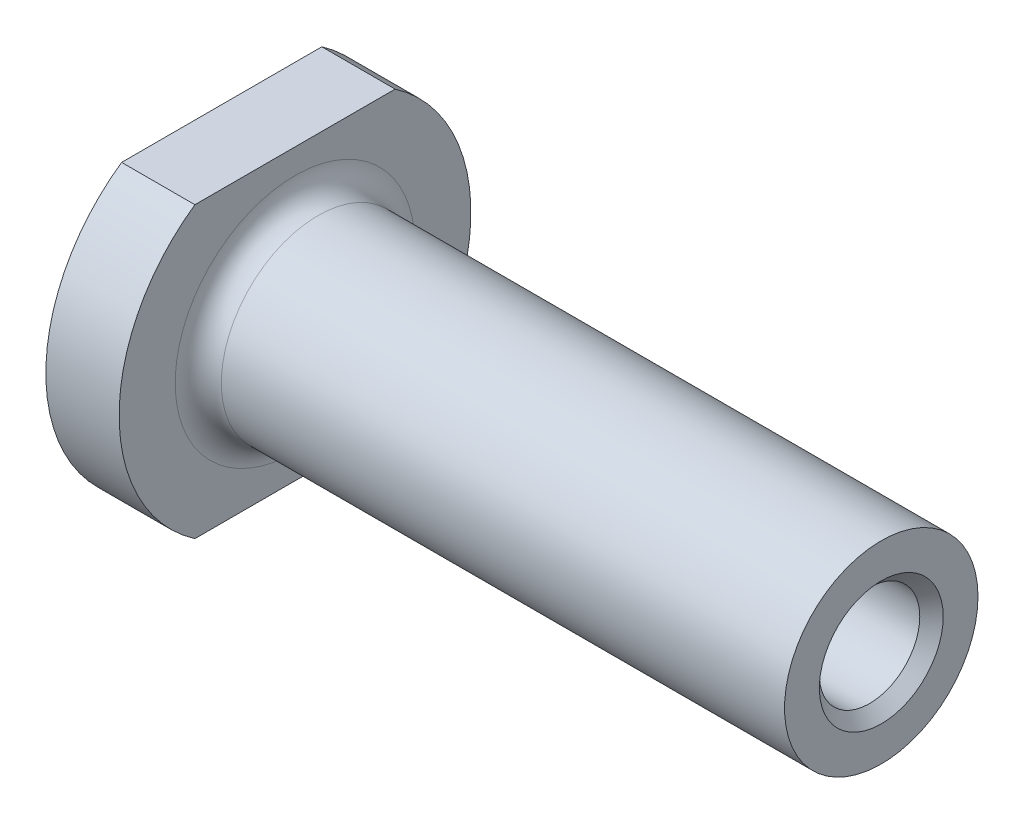
SolidWorks part; units mm, degrees
material "Alloy Steel"
ref_plane "Front Plane" through (0, 0, 0) normal (0, 0, 1) x (1, 0, 0)
ref_plane "Top Plane" through (0, 0, 0) normal (0, 1, 0) x (1, 0, 0)
ref_plane "Right Plane" through (0, 0, 0) normal (1, 0, 0) x (0, 0, -1)
sketch "Sketch1" plane through (0, 0, 0) normal (0, 0, 1) x (1, 0, 0)
  line L0 (0, 0) -> (-17.6508, 0) construction
  line L1 (0, 0) -> (42.8625, 0)
  line L2 (42.8625, 0) -> (42.8625, 6.2865)
  line L3 (42.8625, 6.2865) -> (4.7625, 6.2865)
  line L4 (4.7625, 6.2865) -> (4.7625, 11.43)
  line L5 (4.7625, 11.43) -> (0, 11.43)
  line L6 (0, 11.43) -> (0, 0)
  dimension "D1" = 12.573
  dimension "D2" = 42.8625
  dimension "D3" = 4.7625
  dimension "D4" = 22.86
revolve "Revolve1" add sketch "Sketch1" angle 360 about L0
fillet "Fillet1" radius 1.5 1 edges at (4.7625, 0, -6.2865)
hole_wizard "5/16-18" positions "Sketch2" profile "Sketch3" tap size "5/16-18" standard "ANSI Inch" end condition through all
sketch "Sketch2" plane through (42.8625, 0, 0) normal (1, 0, 0) x (0, 0, -1)
  point P0 (0, 0)
sketch "Sketch3" plane through (42.8625, 0, 0) normal (0, 1, 0) x (0, 0, -1)
  line L0 (0, 0) -> (0, 42.8625)
  line L1 (0, 42.8625) -> (3.2639, 42.8625)
  line L2 (3.2639, 42.8625) -> (3.2639, 0)
  line L5 (3.2639, 0) -> (0, 0)
  line L11 (0, -6.35) -> (0, 107.95) construction
  dimension "Thru Tap Drill Dia." = 6.5278
  dimension "Thru Tap Drill Depth" = 42.8625
cosmetic thread "Hole Thread1" parameters "D2"=7.9375
sketch "Sketch4" plane through (0, 0, 0) normal (-1, 0, 0) x (0, 0, 1)
  line L0 (-6.5056, 9.398) -> (6.5056, 9.398)
  line L5 (6.5056, -9.398) -> (-6.5056, -9.398)
  arc A1 (6.5056, 9.398) -> (-6.5056, 9.398) centre (0, 0) ccw
  circle A2 centre (0, 0) radius 11.43
  arc A3 (-6.5056, -9.398) -> (6.5056, -9.398) centre (0, 0) ccw
  point P4 (0, 11.43)
  dimension "D1" = 0
  dimension "D2" = 2.032
extrude "Cut-Extrude1" cut sketch "Sketch4" against normal through all
chamfer "Chamfer1" distance 0.762 angle 45 2 edges at (0, 0, -3.2639) (42.8625, 0, -3.2639)
equation "\"D1@Sketch1\"=0.500000-.005"
